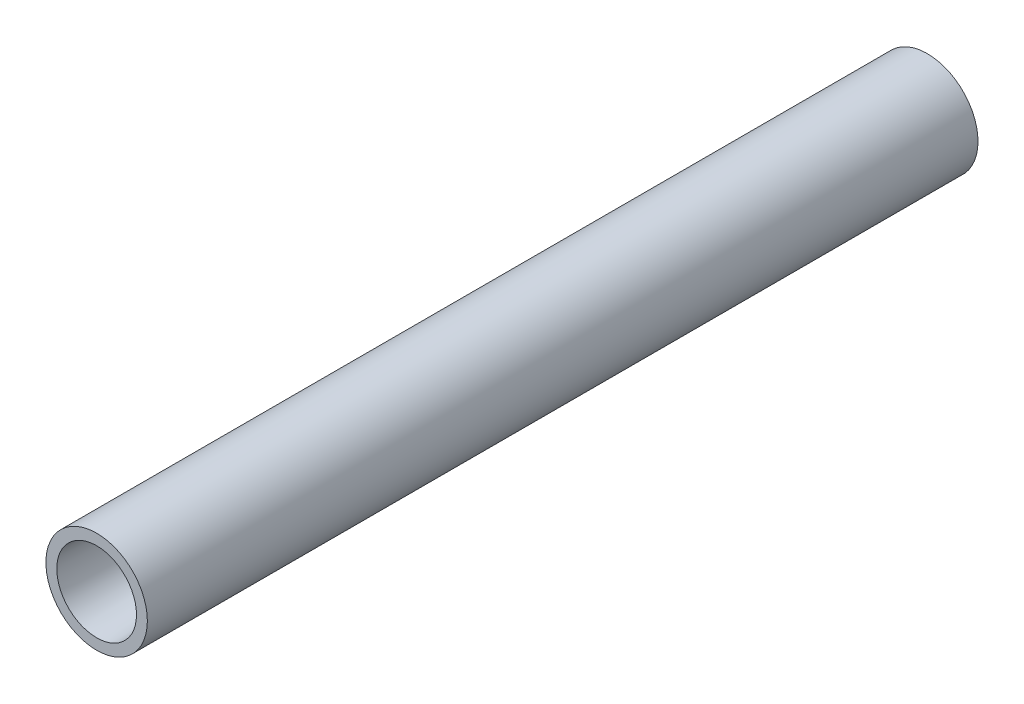
SolidWorks part; units mm, degrees
ref_plane "Front Plane" through (0, 0, 0) normal (0, 0, 1) x (1, 0, 0)
ref_plane "Top Plane" through (0, 0, 0) normal (0, 1, 0) x (1, 0, 0)
ref_plane "Right Plane" through (0, 0, 0) normal (1, 0, 0) x (0, 0, -1)
sketch "Sketch1" plane through (0, 0, 0) normal (0, 0, 1) x (1, 0, 0)
  circle A0 centre (0, 0) radius 4
  dimension "D1" = 8
extrude "Boss-Extrude1" add sketch "Sketch1" along normal blind 65.5
sketch "Sketch2" plane through (0, 0, 0) normal (0, 0, 1) x (1, 0, 0)
  circle A0 centre (0, 0) radius 1
extrude "Cut-Extrude1" cut sketch "Sketch2" along normal through all
sketch "Sketch3" plane through (0, 0, 0) normal (0, 0, 1) x (1, 0, 0)
  circle A0 centre (0, 0) radius 3.1433
  dimension "D1" = 6.2865
extrude "Cut-Extrude2" cut sketch "Sketch3" along normal blind 9.0297 draft 2.328
sketch "Sketch4" plane through (0, 0, 65.5) normal (0, 0, 1) x (1, 0, 0)
  circle A0 centre (0, 0) radius 3.1433
  circle A1 centre (0, 0) radius 3.1433 construction
extrude "Cut-Extrude3" cut sketch "Sketch4" against normal blind 9.0297 draft 2.328 contours A0
